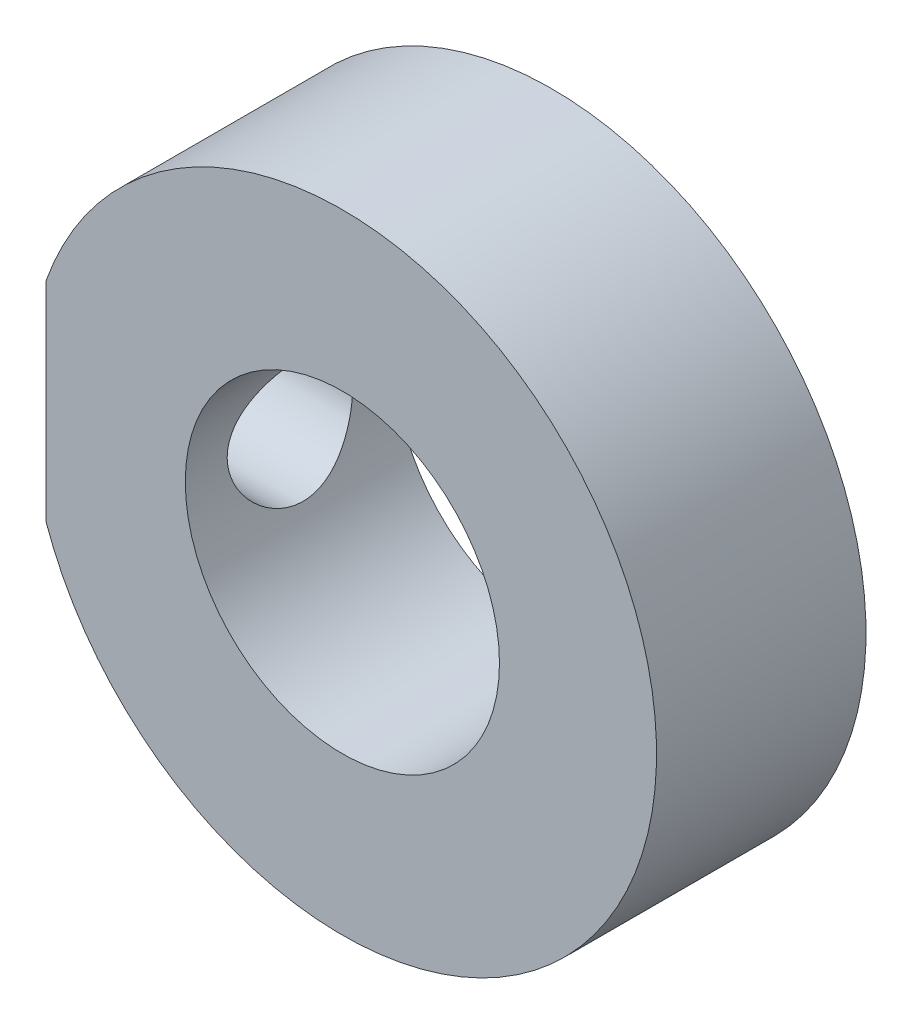
SolidWorks part; units mm, degrees
material "ABS PC"
ref_plane "Ebene vorne" through (0, 0, 0) normal (0, 0, 1) x (1, 0, 0)
ref_plane "Ebene oben" through (0, 0, 0) normal (0, 1, 0) x (1, 0, 0)
ref_plane "Ebene rechts" through (0, 0, 0) normal (1, 0, 0) x (0, 0, -1)
sketch "Skizze1" plane through (0, 0, 0) normal (0, 0, 1) x (1, 0, 0)
  circle A0 centre (0, 0) radius 15
  circle A1 centre (0, 0) radius 7.5
  dimension "D1" = 30
  dimension "D2" = 15
extrude "Aufsatz-Linear austragen1" add sketch "Skizze1" along normal mid plane 10
sketch "Skizze2" plane through (0, 0, 5) normal (0, 0, 1) x (1, 0, 0)
  line L0 (-14.1421, 5) -> (-14.1421, -5)
  circle A0 centre (0, 0) radius 15 construction
  arc A1 (-14.1421, -5) -> (-14.1421, 5) centre (0, 0) cw
  dimension "D1" = 10
extrude "Schnitt-Linear austragen1" cut sketch "Skizze2" against normal through all
sketch "Skizze3" plane through (-14.1421, 0, 0) normal (-1, 0, 0) x (0, 0, 1)
  circle A0 centre (0, 0) radius 3
  dimension "D1" = 6
extrude "Schnitt-Linear austragen2" cut sketch "Skizze3" against normal up to next
